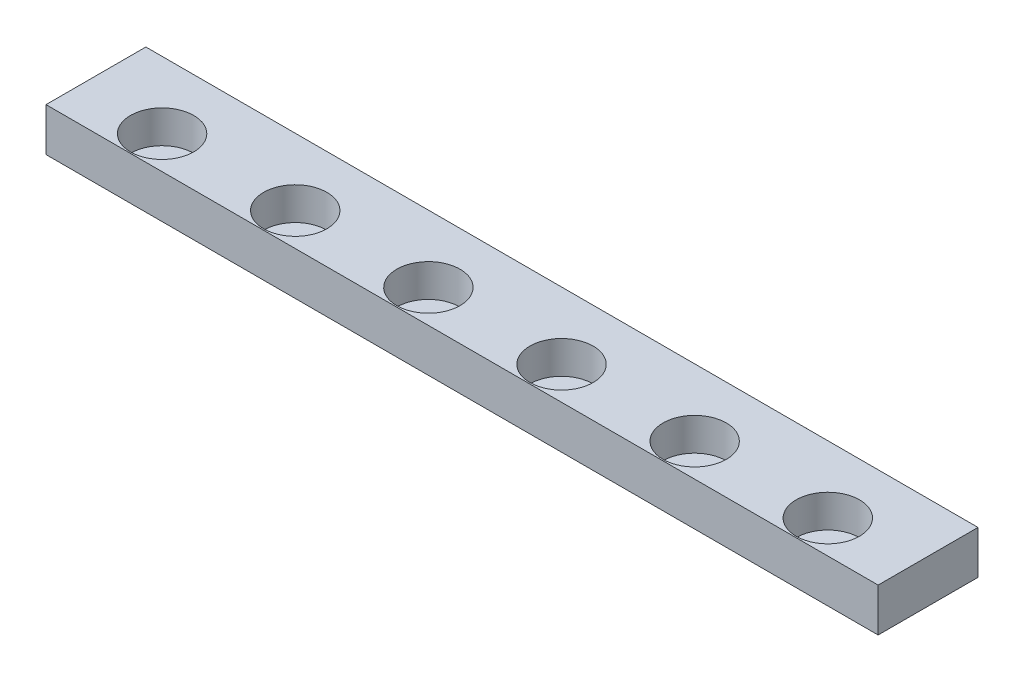
SolidWorks part; units mm, degrees
ref_plane "Front Plane" through (0, 0, 0) normal (0, 0, 1) x (1, 0, 0)
ref_plane "Top Plane" through (0, 0, 0) normal (0, 1, 0) x (1, 0, 0)
ref_plane "Right Plane" through (0, 0, 0) normal (1, 0, 0) x (0, 0, -1)
sketch "Sketch1" plane through (0, 0, 0) normal (0, 1, 0) x (1, 0, 0)
  line L1 (31.75, -3.81) -> (-31.75, -3.81)
  line L2 (31.75, -3.81) -> (31.75, 3.81)
  line L3 (31.75, 3.81) -> (-31.75, 3.81)
  line L4 (-31.75, -3.81) -> (-31.75, 3.81)
  line L5 (31.75, -3.81) -> (-31.75, 3.81) construction
  line L6 (31.75, 3.81) -> (-31.75, -3.81) construction
  point P0 (0, 0)
  dimension "D1" = 7.62
  dimension "D2" = 63.5
extrude "Boss-Extrude1" add sketch "Sketch1" along normal blind 3.302
sketch "Sketch3" plane through (0, 3.302, 0) normal (0, 1, 0) x (1, 0, 0)
  line L0 (-31.75, 0) -> (31.75, 0) construction
  line L1 (-31.75, 3.81) -> (-31.75, -3.81) construction
  line L2 (31.75, -3.81) -> (31.75, 3.81) construction
  line L3 (0, 3.81) -> (0, -3.81) construction
  line L4 (31.75, 3.81) -> (-31.75, 3.81) construction
  line L5 (-31.75, -3.81) -> (31.75, -3.81) construction
  circle A0 centre (-5.08, -1.3) radius 2.413
  circle A1 centre (5.08, -1.3) radius 2.413
  circle A2 centre (15.24, -1.3) radius 2.413
  circle A3 centre (25.4, -1.3) radius 2.413
  circle A4 centre (-15.24, -1.3) radius 2.413
  circle A5 centre (-25.4, -1.3) radius 2.413
  dimension "D3" = 4.826
  dimension "D4" = 3
  dimension "D2" = 5.08
  dimension "D6" = 6.35
  dimension "D7" = 36.83
  dimension "D8" = 46.99
  dimension "D9" = 1.3
  dimension "D1" = 2
  dimension "D5" = 3
extrude "Cut-Extrude3" cut sketch "Sketch3" against normal blind 2.5
